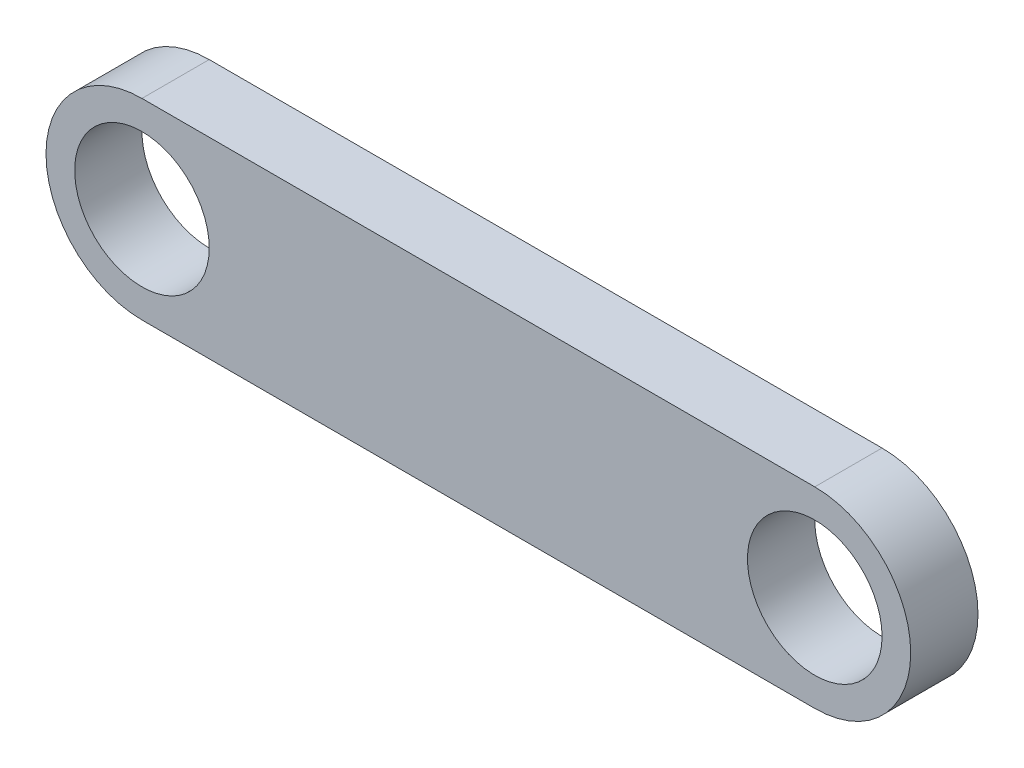
SolidWorks part; units mm, degrees
ref_plane "Front Plane" through (0, 0, 0) normal (0, 0, 1) x (1, 0, 0)
ref_plane "Top Plane" through (0, 0, 0) normal (0, 1, 0) x (1, 0, 0)
ref_plane "Right Plane" through (0, 0, 0) normal (1, 0, 0) x (0, 0, -1)
sketch "Sketch1" plane through (0, 0, 0) normal (0, 0, 1) x (1, 0, 0)
  line L0 (0, 0) -> (50, 0) construction
  line L1 (0, 7.1303) -> (50, 7.1303)
  line L2 (0, -7.1303) -> (50, -7.1303)
  arc A0 (0, 7.1303) -> (0, -7.1303) centre (0, 0) ccw
  arc A1 (50, -7.1303) -> (50, 7.1303) centre (50, 0) ccw
  circle A2 centre (0, 0) radius 5
  circle A3 centre (50, 0) radius 5
  point P3 (25, 0)
  dimension "D2" = 10
  dimension "D3" = 10
  dimension "D1" = 50
extrude "Boss-Extrude2" add sketch "Sketch1" along normal blind 5
